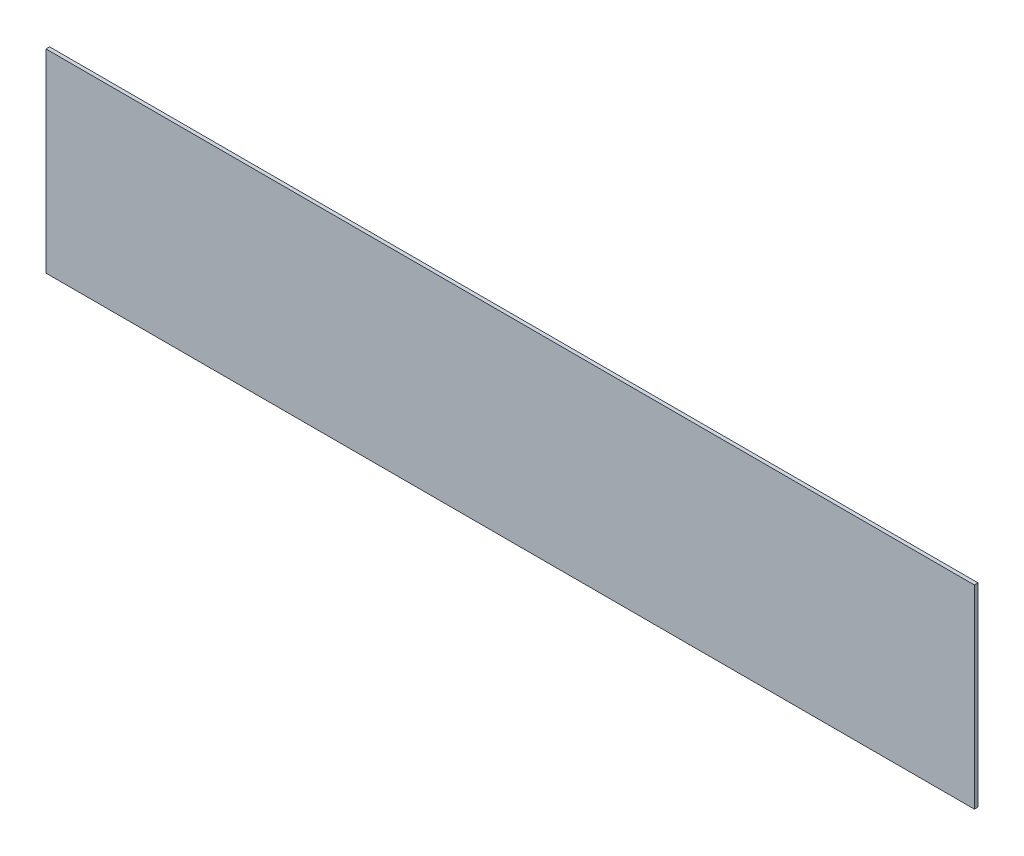
SolidWorks part; units mm, degrees
material "Glass"
ref_plane "Front Plane" through (0, 0, 0) normal (0, 0, 1) x (1, 0, 0)
ref_plane "Top Plane" through (0, 0, 0) normal (0, 1, 0) x (1, 0, 0)
ref_plane "Right Plane" through (0, 0, 0) normal (1, 0, 0) x (0, 0, -1)
sketch "Sketch1" plane through (0, 0, 0) normal (0, 0, 1) x (1, 0, 0)
  line L1 (-607.2187, 127) -> (607.2188, 127)
  line L2 (-607.2187, 127) -> (-607.2187, -127)
  line L3 (-607.2187, -127) -> (607.2188, -127)
  line L4 (607.2188, 127) -> (607.2188, -127)
  line L5 (-607.2187, 127) -> (607.2188, -127) construction
  line L6 (-607.2187, -127) -> (607.2188, 127) construction
  point P0 (0, 0)
  dimension "D1" = 1214.4375
  dimension "D2" = 254
extrude "Boss-Extrude1" add sketch "Sketch1" along normal blind 4.7625
